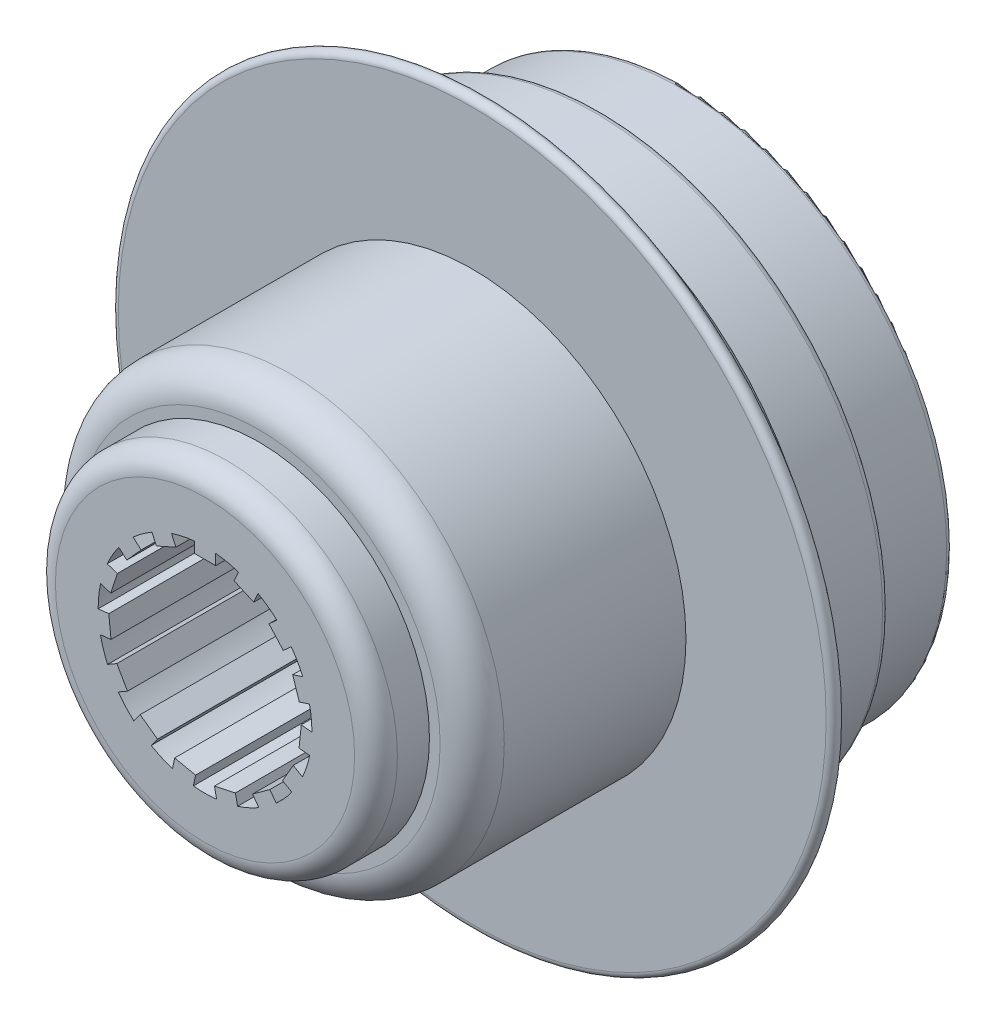
SolidWorks part; units mm, degrees
material "6061 Alloy"
ref_plane "Front Plane" through (0, 0, 0) normal (0, 0, 1) x (1, 0, 0)
ref_plane "Top Plane" through (0, 0, 0) normal (0, 1, 0) x (1, 0, 0)
ref_plane "Right Plane" through (0, 0, 0) normal (1, 0, 0) x (0, 0, -1)
sketch "Sketch1" plane through (0, 0, 0) normal (1, 0, 0) x (0, 0, -1)
  line L0 (0, 0) -> (50000, 0) construction
  line L1 (0, 0) -> (0, 50000) construction
  line L2 (25.4, 0) -> (25.4, 30.988)
  line L3 (24.638, 31.75) -> (15.24, 31.75)
  line L4 (15.24, 31.75) -> (15.24, 33.528)
  line L5 (14.478, 34.29) -> (7.4059, 34.29)
  line L6 (7.4059, 34.29) -> (1.3765, 42.5111)
  line L7 (25.4, 0) -> (-31.75, 0)
  line L8 (0, 42.0604) -> (0, 25.4)
  line L9 (0, 25.4) -> (-21.59, 25.4)
  line L10 (-25.4, 21.59) -> (-25.4, 20.32)
  line L11 (-25.4, 20.32) -> (-29.21, 20.32)
  line L12 (-31.75, 17.78) -> (-31.75, 0)
  arc A0 (25.4, 30.988) -> (24.638, 31.75) centre (24.638, 30.988) ccw
  arc A1 (15.24, 33.528) -> (14.478, 34.29) centre (14.478, 33.528) ccw
  arc A2 (0, 42.0604) -> (1.3765, 42.5111) centre (0.762, 42.0604) cw
  arc A3 (-29.21, 20.32) -> (-31.75, 17.78) centre (-29.21, 17.78) ccw
  arc A4 (-25.4, 21.59) -> (-21.59, 25.4) centre (-21.59, 21.59) cw
  point P20 (15.24, 34.29)
  point P23 (0, 44.3878)
  dimension "D11" = 0.762
  dimension "D12" = 2.54
  dimension "D13" = 3.81
  dimension "D1" = 25.4
  dimension "D2" = 31.75
  dimension "D3" = 34.29
  dimension "D4" = 10.16
  dimension "D5" = 7.8341
  dimension "D6" = 44.3878
  dimension "D7" = 25.4
  dimension "D8" = 20.32
  dimension "D9" = 31.75
  dimension "D10" = 25.4
revolve "Revolve1" add sketch "Sketch1" angle 360 about L0
sketch "Sketch2" plane through (0, 0, -25.4) normal (0, 0, -1) x (-1, 0, 0)
  circle A0 centre (0, 0) radius 19.05
  dimension "D1" = 38.1
extrude "Cut-Extrude1" cut sketch "Sketch2" against normal blind 10.16
sketch "Sketch3" plane through (0, 0, 31.75) normal (0, 0, 1) x (1, 0, 0)
  line L0 (0, 0) -> (0, 15.2091) construction
  line L1 (-1.27, 11.3663) -> (1.27, 11.3663)
  line L2 (1.27, 11.3663) -> (1.27, 12.6363)
  line L3 (-1.27, 11.3663) -> (-1.27, 12.6363)
  line L4 (5.7833, 9.8671) -> (6.2999, 11.0273)
  line L5 (3.4629, 10.9002) -> (3.9795, 12.0604)
  line L6 (3.4629, 10.9002) -> (5.7833, 9.8671)
  line L7 (9.2966, 6.6618) -> (10.2404, 7.5116)
  line L8 (7.597, 8.5494) -> (8.5408, 9.3992)
  line L9 (7.597, 8.5494) -> (9.2966, 6.6618)
  line L10 (11.2025, 2.3046) -> (12.4103, 2.697)
  line L11 (10.4176, 4.7202) -> (11.6254, 5.1127)
  line L12 (10.4176, 4.7202) -> (11.2025, 2.3046)
  line L13 (11.1713, -2.4511) -> (12.4344, -2.5839)
  line L14 (11.4368, 0.0749) -> (12.6999, -0.0578)
  line L15 (11.4368, 0.0749) -> (11.1713, -2.4511)
  line L16 (9.2085, -6.783) -> (10.3084, -7.418)
  line L17 (10.4785, -4.5833) -> (11.5784, -5.2183)
  line L18 (10.4785, -4.5833) -> (9.2085, -6.783)
  line L19 (5.6535, -9.942) -> (6.4, -10.9695)
  line L20 (7.7084, -8.4491) -> (8.4549, -9.4765)
  line L21 (7.7084, -8.4491) -> (5.6535, -9.942)
  line L22 (1.1209, -11.382) -> (1.385, -12.6243)
  line L23 (3.6054, -10.8539) -> (3.8695, -12.0962)
  line L24 (3.6054, -10.8539) -> (1.1209, -11.382)
  line L25 (-3.6054, -10.8539) -> (-3.8695, -12.0962)
  line L26 (-1.1209, -11.382) -> (-1.385, -12.6243)
  line L27 (-1.1209, -11.382) -> (-3.6054, -10.8539)
  line L28 (-7.7084, -8.4491) -> (-8.4549, -9.4765)
  line L29 (-5.6535, -9.942) -> (-6.4, -10.9695)
  line L30 (-5.6535, -9.942) -> (-7.7084, -8.4491)
  line L31 (-10.4785, -4.5833) -> (-11.5784, -5.2183)
  line L32 (-9.2085, -6.783) -> (-10.3084, -7.418)
  line L33 (-9.2085, -6.783) -> (-10.4785, -4.5833)
  line L34 (-11.4368, 0.0749) -> (-12.6999, -0.0578)
  line L35 (-11.1713, -2.4511) -> (-12.4344, -2.5839)
  line L36 (-11.1713, -2.4511) -> (-11.4368, 0.0749)
  line L37 (-10.4176, 4.7202) -> (-11.6254, 5.1127)
  line L38 (-11.2025, 2.3046) -> (-12.4103, 2.697)
  line L39 (-11.2025, 2.3046) -> (-10.4176, 4.7202)
  line L40 (-7.597, 8.5494) -> (-8.5408, 9.3992)
  line L41 (-9.2966, 6.6618) -> (-10.2404, 7.5116)
  line L42 (-9.2966, 6.6618) -> (-7.597, 8.5494)
  line L43 (-3.4629, 10.9002) -> (-3.9795, 12.0604)
  line L44 (-5.7833, 9.8671) -> (-6.2999, 11.0273)
  line L45 (-5.7833, 9.8671) -> (-3.4629, 10.9002)
  arc A0 (-10.2404, 7.5116) -> (-11.6254, 5.1127) centre (0, 0) ccw
  arc A1 (-6.2999, 11.0273) -> (-8.5408, 9.3992) centre (0, 0) ccw
  arc A2 (-1.27, 12.6363) -> (-3.9795, 12.0604) centre (0, 0) ccw
  arc A3 (3.9795, 12.0604) -> (1.27, 12.6363) centre (0, 0) ccw
  arc A4 (8.5408, 9.3992) -> (6.2999, 11.0273) centre (0, 0) ccw
  arc A5 (11.6254, 5.1127) -> (10.2404, 7.5116) centre (0, 0) ccw
  arc A6 (12.6999, -0.0578) -> (12.4103, 2.697) centre (0, 0) ccw
  arc A7 (11.5784, -5.2183) -> (12.4344, -2.5839) centre (0, 0) ccw
  arc A8 (8.4549, -9.4765) -> (10.3084, -7.418) centre (0, 0) ccw
  arc A9 (3.8695, -12.0962) -> (6.4, -10.9695) centre (0, 0) ccw
  arc A10 (-6.4, -10.9695) -> (-3.8695, -12.0962) centre (0, 0) ccw
  arc A11 (-1.385, -12.6243) -> (1.385, -12.6243) centre (0, 0) ccw
  arc A12 (-10.3084, -7.418) -> (-8.4549, -9.4765) centre (0, 0) ccw
  arc A13 (-12.4344, -2.5839) -> (-11.5784, -5.2183) centre (0, 0) ccw
  arc A14 (-12.4103, 2.697) -> (-12.6999, -0.0578) centre (0, 0) ccw
  point P9 (0, 11.3663)
  dimension "D1" = 25.4
  dimension "D2" = 1.27
  dimension "D3" = 1.27
  dimension "D4" = 15
extrude "Cut-Extrude4" cut sketch "Sketch3" against normal blind 35.56
